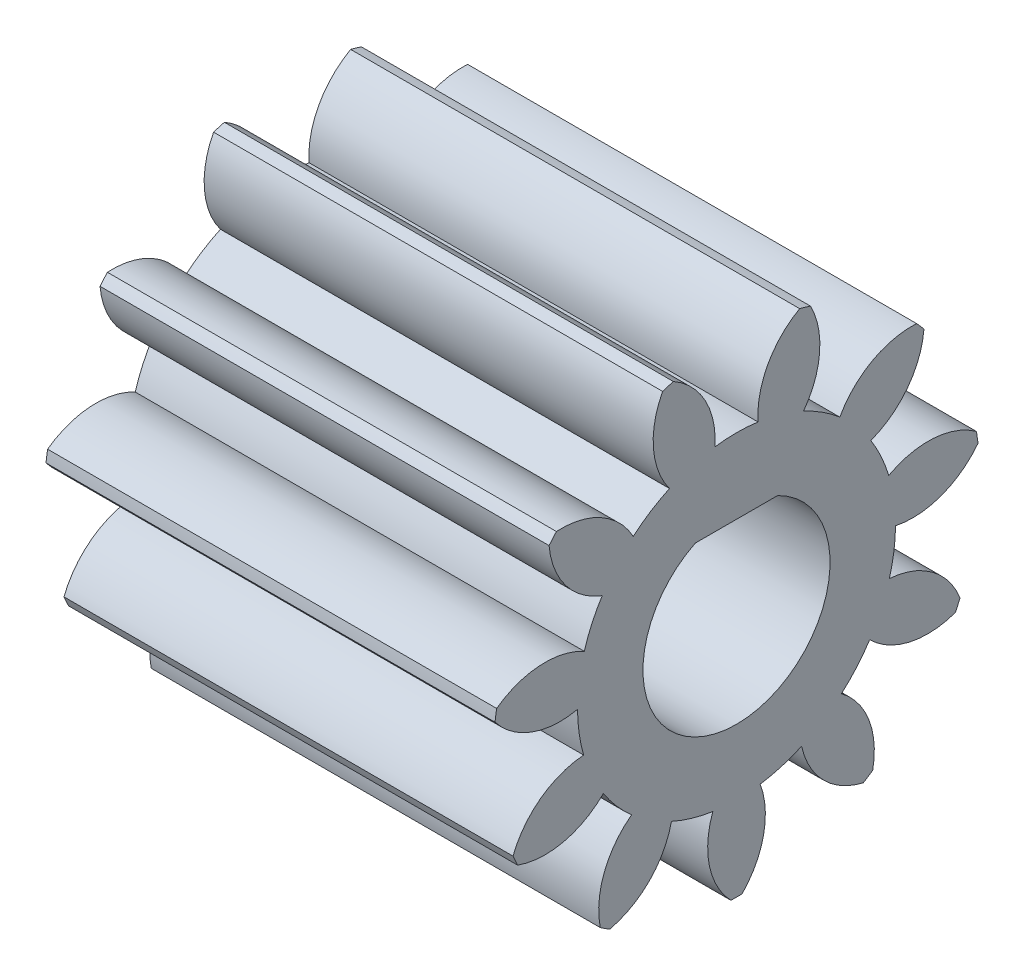
SolidWorks part; units mm, degrees
ref_plane "Plane1" through (0, 0, 0) normal (0, 0, 1) x (1, 0, 0)
ref_plane "Plane2" through (0, 0, 0) normal (0, 1, 0) x (1, 0, 0)
ref_plane "Plane3" through (0, 0, 0) normal (1, 0, 0) x (0, 0, -1)
sketch "HoldingSke" plane through (0, 0, 0) normal (0, 1, 0) x (1, 0, 0)
  line L0 (0, 0) -> (0.9816, -0.1908)
  line L1 (-15, 0) -> (100, 0) construction
  line L2 (0, 0) -> (-2.1039, 2.3779)
  line L3 (0, 0) -> (-11.863, 4.5341)
  line L4 (0, 0) -> (8.4773, 1.6478)
  line L5 (0, 0) -> (-46.8476, -17.4728)
  line L6 (0, 0) -> (-9.9476, -6.7116)
  line L7 (-2.1039, 2.3779) -> (8.6586, 51.2059)
  line L8 (-76.2, 54.61) -> (-75.3, 54.61)
  line L9 (-71.009, 38.7566) -> (-53.1078, 45.2721)
  line L10 (-76.2, 71.12) -> (104.1128, 71.12)
  line L11 (0, 0) -> (-12, 0)
  line L12 (-76.2, 101.6) -> (-76.162, 101.6)
  line L13 (24.9733, 27.94) -> (52.9518, 28.4284)
  line L14 (24.9733, 27.94) -> (24.9743, 27.94)
  line L15 (24.9733, 27.94) -> (100.4006, 29.5858)
  line L16 (-63.627, -1) -> (-12.827, -1)
  circle A0 centre (0, 0) radius 2.5
  circle A1 centre (0, 0) radius 4.249
  circle A2 centre (0, 0) radius 37.5
  circle A3 centre (0, 0) radius 2.5
  dimension "MHD" = 8.498
  dimension "Hub_dia" = 75
  dimension "Bore" = 5
  dimension "MBD" = 5
  dimension "Num_teeth" = 11
  dimension "Pitch" = 1
  dimension "Overall_len" = 50
  dimension "Show_teeth" = 11
  dimension "Thickness" = 12
  dimension "OAL" = 50.0001
  dimension "T_dim" = 0.9
  dimension "Ap" = 20
  dimension "H" = 19.05
  dimension "Pitch_radius" = 180.3128
  dimension "Width" = 12
  dimension "Backlash" = 0.038
  dimension "Addendum_fac" = 1
  dimension "Dedendum_fac" = 1.25
  dimension "Clearance_fac" = 0.25
  dimension "Dedendum_add" = 0.001
  dimension "Module" = 1
sketch "BasProSke" plane through (0, 0, 0) normal (0, 1, 0) x (1, 0, 0)
  line L0 (-10, 0) -> (60, 0) construction
  line L1 (0, 0) -> (0, 6.5)
  line L2 (0, 0) -> (12, 0)
  line L3 (12, 0) -> (12, 6.5)
  line L4 (12, 6.5) -> (0, 6.5)
  dimension "Thickness" = 12
  dimension "Diameter" = 13
revolve "Base-Revolve" add sketch "BasProSke" angle 360 about L0
sketch "TooCutSke" plane through (0, 0, 0) normal (1, 0, 0) x (0, 0, -1)
  line L1 (0, 0) -> (0, 107) construction
  line L2 (0, 0) -> (-0.8491, 5.4341) construction
  line L3 (0, 0) -> (-3.0727, 10.4645) construction
  line L4 (-0.8491, 5.4341) -> (-1.5363, 5.2323) construction
  arc A0 (0.576, 4.2098) -> (-0.576, 4.2098) centre (0, 0) ccw
  arc A1 (1.7187, 6.295) -> (-1.7187, 6.295) centre (0, 0) ccw
  circle A2 centre (0, 0) radius 5.5 construction
  circle A3 centre (0, 0) radius 5.1683 construction
  arc A4 (-0.576, 4.2098) -> (-1.7187, 6.295) centre (-2.7707, 4.3629) ccw
  arc A5 (1.7187, 6.295) -> (0.576, 4.2098) centre (2.7707, 4.3629) ccw
  dimension "Root_dia" = 8.498
  dimension "Overcut_dia" = 13.0508
  dimension "Pitch_dia" = 11
  dimension "Base_dia" = 10.3366
  dimension "Flank_rad" = 2.2
  dimension "Half_ang" = 16.364
  dimension "Half_CT" = 0.7162
extrude "ToothCut" cut sketch "TooCutSke" along normal through all
fillet "Breaks" [suppressed] radius 0.02
fillet "RootFillets" [suppressed] radius 0.251
pattern_circular "TeethCuts" count 11 every 32.727 about axis through (-10, 0, 0) along (1, 0, 0) of "ToothCut", "RootFillets", "Breaks"
sketch "HubNeaOneSke" plane through (0, 0, 0) normal (-1, 0, 0) x (0, 0, 1)
  circle A0 centre (0, 0) radius 4.249
  dimension "Diameter" = 8.498
extrude "HubNearOne" [suppressed] add sketch "HubNeaOneSke" along normal blind 38.0001
sketch "HubNeaBotSke" plane through (0, 0, 0) normal (-1, 0, 0) x (0, 0, 1)
  circle A0 centre (0, 0) radius 4.249
  dimension "Diameter" = 8.498
extrude "HubNearBoth" [suppressed] add sketch "HubNeaBotSke" along normal blind 19
ref_plane "FarPln" through (12, 0, 0) normal (1, 0, 0) x (0, 0, -1)
sketch "HubFarSke" plane through (12, 0, 0) normal (1, 0, 0) x (0, 0, -1)
  circle A0 centre (0, 0) radius 4.249
  dimension "Diameter" = 8.498
extrude "HubFar" [suppressed] add sketch "HubFarSke" along normal blind 19
sketch "BorSke" plane through (0, 0, 0) normal (1, 0, 0) x (0, 0, -1)
  circle A0 centre (0, 0) radius 2.5
  dimension "Diameter" = 5
extrude "Bore" cut sketch "BorSke" along normal mid plane 100.0001
sketch "KeySke" plane through (0, 0, 0) normal (1, 0, 0) x (0, 0, -1)
  line L0 (-1, 0) -> (-1, 3.4)
  line L1 (-1, 3.4) -> (1, 3.4)
  line L2 (1, 3.4) -> (1, 0)
  line L3 (0, 0) -> (0, 34) construction
  line L4 (-1, 0) -> (1, 0)
  dimension "Offset" = 3.4
  dimension "Width" = 2
extrude "Keyway" [suppressed] cut sketch "KeySke" along normal mid plane 100.0001
pattern_circular "Keyway2" [suppressed] count 2 every 90 about axis through (-10, 0, 0) along (1, 0, 0)
sketch "Sketch1" plane through (12, 0, 0) normal (1, 0, 0) x (0, 0, -1)
  line L0 (-1.1, 2.245) -> (1.1, 2.245)
  circle A0 centre (0, 0) radius 2.5 construction
  circle A2 centre (0, 0) radius 2.5
  arc A3 (1.1, 2.245) -> (-1.1, 2.245) centre (0, 0) ccw
  point P4 (0, 0)
  dimension "D1" = 0
extrude "Boss-Extrude1" add sketch "Sketch1" against normal blind 12
equation "' \"Module@HoldingSke\" = 6.35"
equation "' \"Num_teeth@HoldingSke\" = 12"
equation "' \"Ap@HoldingSke\" =  20"
equation "' \"Ap@HoldingSke\" = 20"
equation "' \"Width@HoldingSke\" = 0.5 * 25.4"
equation "' \"Hub_dia@HoldingSke\"= 1 * 25.4"
equation "' \"Hub_dia@HoldingSke\" = 1 * 25.4"
equation "' \"Overall_len@HoldingSke\" = 1.0 * 25.4"
equation "' \"Bore@HoldingSke\" = 0.75 * 25.4"
equation "' \"T_dim@HoldingSke\" = 0.1 * 25.4"
equation "' \"Width@KeySke\" = 0.25 * 25.4"
equation "' \"Show_teeth@HoldingSke\" = 13"
equation "' \"Backlash@HoldingSke\" = 0.009 * 25.4"
equation "' \"Addendum_fac@HoldingSke\" = 1.0"
equation "' \"Dedendum_fac@HoldingSke\" = 1.25"
equation "' \"Dedendum_add@HoldingSke\" = 0.00005 * 25.4"
equation "' \"Clearance_fac@HoldingSke\" = 0.25"
equation "\"Pitch@HoldingSke\" = 1 / \"Module@HoldingSke\""
equation "\"Overcut_dia@TooCutSke\" = (\"Num_teeth@HoldingSke\" + 2 * \"Addendum_fac@HoldingSke\") / \"Pitch@HoldingSke\" + 0.002 * 25.4"
equation "\"Pitch_dia@TooCutSke\" = \"Num_teeth@HoldingSke\" / \"Pitch@HoldingSke\""
equation "\"Base_dia@TooCutSke\" = \"Num_teeth@HoldingSke\" / \"Pitch@HoldingSke\" * cos((\"Ap@HoldingSke\"  * 3.14159265 / 180))"
equation "\"Root_dia@TooCutSke\" = (\"Num_teeth@HoldingSke\" + 2) / \"Pitch@HoldingSke\" - 2 * (\"Addendum_fac@HoldingSke\" + \"Dedendum_fac@HoldingSke\") / \"Pitch@HoldingSke\" - \"Dedendum_add@HoldingSke\" * 2"
equation "\"Half_ang@TooCutSke\" = 180 / \"Num_teeth@HoldingSke\""
equation "\"Half_CT@TooCutSke\" = \"Num_teeth@HoldingSke\" / \"Pitch@HoldingSke\" * sin((3.14159265 / 2 / \"Num_teeth@HoldingSke\")) / 2 - 7 * \"Backlash@HoldingSke\" / 4"
equation "\"Flank_rad@TooCutSke\" = \"Num_teeth@HoldingSke\" / \"Pitch@HoldingSke\" / 5"
equation "\"Radius@RootFillets\" = \"Clearance_fac@HoldingSke\" / \"Pitch@HoldingSke\" + \"Dedendum_add@HoldingSke\""
equation "\"Break_rad@Breaks\" = 0.02 / \"Pitch@HoldingSke\""
equation "\"Thickness@HoldingSke\" = \"Width@HoldingSke\""
equation "\"OAL@HoldingSke\" = \"Thickness@HoldingSke\""
equation "\"MHD@HoldingSke\" = (\"Num_teeth@HoldingSke\" + 2) / \"Pitch@HoldingSke\" - 2 * (\"Addendum_fac@HoldingSke\" + \"Dedendum_fac@HoldingSke\")  / \"Pitch@HoldingSke\" - \"Dedendum_add@HoldingSke\" * 2"
equation "\"MBD@HoldingSke\" = (\"Num_teeth@HoldingSke\" + 2) / \"Pitch@HoldingSke\" - 2 * (\"Addendum_fac@HoldingSke\" + \"Dedendum_fac@HoldingSke\")  / \"Pitch@HoldingSke\" - \"Dedendum_add@HoldingSke\" * 2 - 0.002 * 25.4"
equation "\"MHD@HoldingSke\" = ((sgn( \"MHD@HoldingSke\" - \"Hub_dia@HoldingSke\" )-1)*( \"MHD@HoldingSke\" - \"Hub_dia@HoldingSke\" ))/-2+ \"Hub_dia@HoldingSke\""
equation "\"MBD@HoldingSke\" = ((sgn( \"MBD@HoldingSke\" - \"Bore@HoldingSke\" )-1)*( \"MBD@HoldingSke\" - \"Bore@HoldingSke\" ))/-2+ \"Bore@HoldingSke\""
equation "\"OAL@HoldingSke\" = ((sgn( \"OAL@HoldingSke\" - \"Overall_len@HoldingSke\" )+1)*( \"OAL@HoldingSke\" - \"Overall_len@HoldingSke\" ))/2 + \"Overall_len@HoldingSke\" + 0.000002 * 25.4"
equation "\"Num_teeth@TeethCuts\" = int( \"Show_teeth@HoldingSke\" ) + 1"
equation "\"Num_teeth@TeethCuts\" = ((sgn( \"Num_teeth@TeethCuts\" - \"Num_teeth@HoldingSke\" )-1)*( \"Num_teeth@TeethCuts\" - \"Num_teeth@HoldingSke\" ))/-2+ \"Num_teeth@HoldingSke\""
equation "\"Num_teeth@TeethCuts\" = ((sgn( \"Num_teeth@TeethCuts\" - 2.0)+1)*( \"Num_teeth@TeethCuts\" - 2.0))/2 +2.0"
equation "\"Angle@TeethCuts\" = 360.0 / \"Num_teeth@HoldingSke\""
equation "\"Diameter@BasProSke\" = (\"Num_teeth@HoldingSke\" + 2 * \"Addendum_fac@HoldingSke\") / \"Pitch@HoldingSke\""
equation "\"Thickness@BasProSke\"  = \"Thickness@HoldingSke\""
equation "' \"Fillet_rad@BasProSke\" =  \"Thickness@HoldingSke\" * 0.05"
equation "' \"Fillet_rad@BasProSke\" = \"Thickness@HoldingSke\" * 0.05"
equation "\"MHD@HoldingSke\" = ((sgn( \"MHD@HoldingSke\" - \"Root_dia@TooCutSke\" )-1)*( \"MHD@HoldingSke\" - \"Root_dia@TooCutSke\" ))/-2+ \"Root_dia@TooCutSke\""
equation "\"Diameter@HubNeaOneSke\" = \"MHD@HoldingSke\""
equation "\"Length@HubNearOne\" = \"OAL@HoldingSke\" - \"Thickness@BasProSke\""
equation "\"Diameter@HubNeaBotSke\" = \"MHD@HoldingSke\""
equation "\"Length@HubNearBoth\" = ( \"OAL@HoldingSke\" - \"Thickness@BasProSke\" ) / 2.0"
equation "\"Thickness@FarPln\" = \"Thickness@BasProSke\""
equation "\"Diameter@HubFarSke\" = \"MHD@HoldingSke\""
equation "\"Length@HubFar\" = ( \"OAL@HoldingSke\" - \"Thickness@BasProSke\" ) / 2.0"
equation "\"Diameter@BorSke\" = \"MBD@HoldingSke\""
equation "\"D1@Bore\" = \"OAL@HoldingSke\" * 2.0"
equation "\"D1@Keyway\" = \"OAL@HoldingSke\" * 2.0"
equation "\"Offset@KeySke\" = \"T_dim@HoldingSke\" + \"MBD@HoldingSke\" / 2.0"
